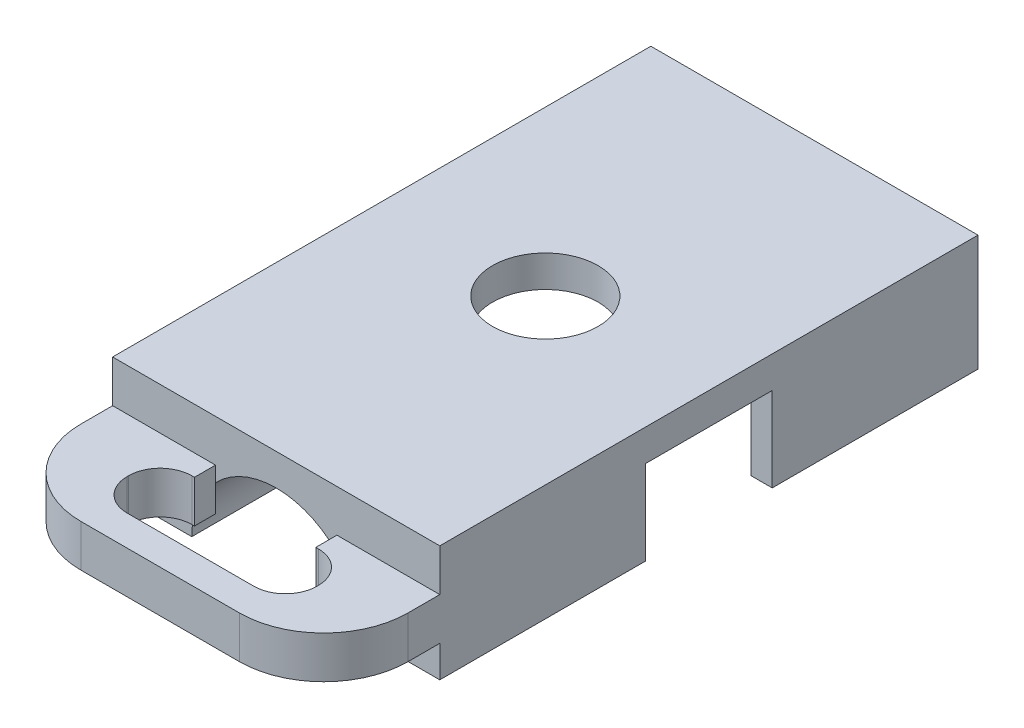
SolidWorks part; units mm, degrees
material "Калифорния"
ref_plane "Спереди" through (0, 0, 0) normal (0, 0, 1) x (1, 0, 0)
ref_plane "Сверху" through (0, 0, 0) normal (0, 1, 0) x (1, 0, 0)
ref_plane "Справа" through (0, 0, 0) normal (1, 0, 0) x (0, 0, -1)
sketch "Эскиз1" plane through (0, 0, 0) normal (0, 1, 0) x (1, 0, 0)
  line L1 (15.5, -25.5) -> (-15.5, -25.5)
  line L2 (15.5, -25.5) -> (15.5, 25.5)
  line L3 (15.5, 25.5) -> (-15.5, 25.5)
  line L4 (-15.5, -25.5) -> (-15.5, 25.5)
  line L5 (15.5, -25.5) -> (-15.5, 25.5) construction
  line L6 (15.5, 25.5) -> (-15.5, -25.5) construction
  point P0 (0, 0)
extrude "Бобышка-Вытянуть1" add sketch "Эскиз1" along normal blind 0.0001 and the other way blind 11
sketch "Эскиз2" plane through (0, -11, 0) normal (0, -1, 0) x (1, 0, 0)
  line L0 (15.5, 25.5) -> (15.5, -25.5) construction
  line L1 (-15.5, 6) -> (15.5, 6)
  line L2 (-15.5, 6) -> (-15.5, -6)
  line L3 (-15.5, -6) -> (15.5, -6)
  line L4 (15.5, 6) -> (15.5, -6)
  line L5 (-15.5, 6) -> (15.5, -6) construction
  line L6 (-15.5, -6) -> (15.5, 6) construction
  line L8 (13.5, -14.5) -> (-13.5, -14.5)
  line L9 (13.5, -14.5) -> (13.5, 14.5)
  line L10 (13.5, 14.5) -> (-13.5, 14.5)
  line L11 (-13.5, -14.5) -> (-13.5, 14.5)
  line L12 (13.5, -14.5) -> (-13.5, 14.5) construction
  line L13 (13.5, 14.5) -> (-13.5, -14.5) construction
  circle A0 centre (0, 0) radius 18
  circle A1 centre (0, 0) radius 5
  line M1 (-15.5, 25.5) -> (-15.5, -25.5)
  line M3 (15.5, -25.5) -> (15.5, 25.5)
extrude "Вырез-Вытянуть1" cut sketch "Эскиз2" against normal blind 8 and the other way blind 0.0001 contours L9 A0 L10 L11 L1 | L11 L3 L9 L1 A1 | L3 L11 L1 M1 | L9 L3 L1 M3 | L8 A0 L9 L3 L11 | A0 L8 L9 | L8 A0 | A0 L11 L8 | A0 L10 L11 | L10 A0 | A0 L9 L10
sketch "Эскиз3" plane through (0, -11, 0) normal (0, -1, 0) x (1, 0, 0)
  circle A0 centre (0, 0) radius 5
extrude "Вырез-Вытянуть3" cut sketch "Эскиз3" against normal blind 12
sketch "Эскиз4" plane through (0, 0, 25.5) normal (0, 0, 1) x (1, 0, 0)
  line L0 (-15.5, -11) -> (15.5, -11) construction
  circle A0 centre (0, -11) radius 8
extrude "Вырез-Вытянуть4" cut sketch "Эскиз4" against normal blind 102
sketch3d "Трехмерный эскиз1"
  line L0 (-15.5, -11, 25.5) -> (-15.5, 0.0001, 25.5) construction
  line L1 (-15.5, -3.9999, 25.5) -> (-5.75, -3.9999, 25.5)
  line L2 (-15.5, -3.9999, 25.5) -> (-15.5, -3.9999, 28.5)
  line L3 (-7.5, -3.9999, 36.5) -> (7.5, -3.9999, 36.5)
  line L4 (15.5, -3.9999, 25.5) -> (15.5, -3.9999, 28.5)
  line L5 (-5.9986, -3.9999, 27.5) -> (-5.75, -3.9999, 27.5)
  line L6 (5.75, -3.9999, 25.5) -> (15.5, -3.9999, 25.5)
  line L7 (5.75, -3.9999, 27.5) -> (5.9986, -3.9999, 27.5)
  line L9 (-5.75, -3.9999, 25.5) -> (-5.75, -3.9999, 27.5)
  line L13 (5.75, -3.9999, 25.5) -> (5.75, -3.9999, 27.5)
  line L15 (5.9986, -3.9999, 33.6254) -> (-5.9986, -3.9999, 33.6254)
  line L16 (8.9986, -3.9999, 30.6254) -> (8.9986, -3.9999, 30.5)
  line L18 (-8.9986, -3.9999, 30.6254) -> (-8.9986, -3.9999, 30.5)
  line L19 (8.9986, -3.9999, 33.6254) -> (-8.9986, -3.9999, 27.5) construction
  line L20 (8.9986, -3.9999, 27.5) -> (-8.9986, -3.9999, 33.6254) construction
  arc A0 (7.5, -3.9999, 36.5) -> (15.5, -3.9999, 28.5) centre (7.5, -3.9999, 28.5) ccw
  arc A1 (-7.5, -3.9999, 36.5) -> (-15.5, -3.9999, 28.5) centre (-7.5, -3.9999, 28.5) ccw
  arc A2 (-5.9986, -3.9999, 27.5) -> (-8.9986, -3.9999, 30.5) centre (-5.9986, -3.9999, 30.5) ccw
  arc A3 (8.9986, -3.9999, 30.5) -> (5.9986, -3.9999, 27.5) centre (5.9986, -3.9999, 30.5) ccw
  arc A4 (5.9986, -3.9999, 33.6254) -> (8.9986, -3.9999, 30.6254) centre (5.9986, -3.9999, 30.6254) ccw
  arc A5 (-5.9986, -3.9999, 33.6254) -> (-8.9986, -3.9999, 30.6254) centre (-5.9986, -3.9999, 30.6254) ccw
  point P8 (15.5, -3.9999, 36.5)
  point P9 (7.5, 4.0001, 28.5)
  point P12 (-15.5, -3.9999, 36.5)
  point P13 (-7.5, -11.9999, 28.5)
  point P27 (-8.9986, -3.9999, 27.5)
  point P29 (-5.9986, -0.9999, 30.5)
  point P32 (8.9986, -3.9999, 27.5)
  point P34 (5.9986, -0.9999, 30.5)
  point P37 (8.9986, -3.9999, 33.6254)
  point P39 (5.9986, -0.9999, 30.6254)
  point P42 (-8.9986, -3.9999, 33.6254)
  point P44 (-5.9986, -6.9999, 30.6254)
  dimension "D2" = 8
  dimension "D3" = 3
  dimension "D1" = 4
extrude "Бобышка-Вытянуть2" add sketch "Трехмерный эскиз1" along direction (0, 1, 0) on the side of the normal blind 4
